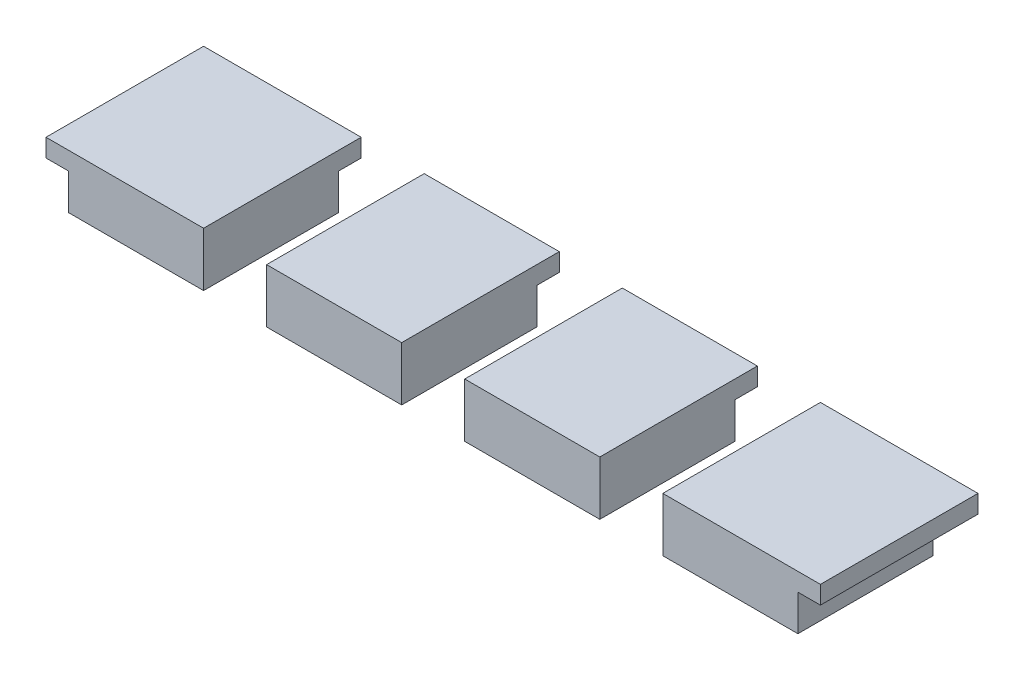
SolidWorks part; units mm, degrees
ref_plane "Front Plane" through (0, 0, 0) normal (0, 0, 1) x (1, 0, 0)
ref_plane "Top Plane" through (0, 0, 0) normal (0, 1, 0) x (1, 0, 0)
ref_plane "Right Plane" through (0, 0, 0) normal (1, 0, 0) x (0, 0, -1)
sketch "Sketch1" plane through (0, 0, 0) normal (0, 1, 0) x (1, 0, 0)
  line L1 (-39.05, -27.95) -> (39.05, -27.95)
  line L2 (-39.05, -27.95) -> (-39.05, 27.95)
  line L3 (-39.05, 27.95) -> (39.05, 27.95)
  line L4 (39.05, -27.95) -> (39.05, 27.95)
  line L5 (-39.05, -27.95) -> (39.05, 27.95) construction
  line L6 (-39.05, 27.95) -> (39.05, -27.95) construction
  point P0 (0, 0)
extrude "Boss-Extrude1" add sketch "Sketch1" along normal blind 3
sketch "Sketch2" plane through (0, 3, 0) normal (0, 1, 0) x (1, 0, 0)
  circle A0 centre (-35.9, 20.9) radius 1.25
  circle A1 centre (-35.9, -24.8) radius 1.25
  circle A2 centre (35.9, -24.8) radius 1.25
  circle A3 centre (35.9, 24.8) radius 1.25
extrude "Cut-Extrude1" cut sketch "Sketch2" against normal blind 68
sketch "Sketch3" plane through (0, 3, 0) normal (0, 1, 0) x (1, 0, 0)
  line L0 (-39.05, -27.95) -> (39.05, -27.95) construction
  line L5 (-31.15, -27.95) -> (8.45, -27.95)
  line L6 (-31.15, -27.95) -> (-31.15, -12.75)
  line L7 (-31.15, -12.75) -> (8.45, -12.75)
  line L8 (8.45, -27.95) -> (8.45, -12.75)
  line L13 (27.35, -17.65) -> (15.85, -17.65)
  line L14 (27.35, -17.65) -> (27.35, -27.95)
  line L15 (27.35, -27.95) -> (15.85, -27.95)
  line L16 (15.85, -17.65) -> (15.85, -27.95)
  line L18 (-39.05, 27.95) -> (39.05, 27.95)
  line L19 (-39.05, 27.95) -> (-39.05, -27.95)
  line L20 (-39.05, -27.95) -> (39.05, -27.95)
  line L21 (39.05, 27.95) -> (39.05, -27.95)
  line L22 (-31.15, -27.95) -> (-25.45, -27.95)
  line L23 (-31.15, -27.95) -> (-31.15, -20.45)
  line L24 (-31.15, -20.45) -> (-25.45, -20.45)
  line L25 (-25.45, -27.95) -> (-25.45, -20.45)
  line L26 (8.45, -27.95) -> (2.75, -27.95)
  line L27 (8.45, -27.95) -> (8.45, -20.45)
  line L28 (8.45, -20.45) -> (2.75, -20.45)
  line L29 (2.75, -27.95) -> (2.75, -20.45)
  line L30 (2.75, -27.95) -> (-6.65, -27.95)
  line L31 (2.75, -27.95) -> (2.75, -20.45)
  line L32 (2.75, -20.45) -> (-6.65, -20.45)
  line L33 (-6.65, -27.95) -> (-6.65, -20.45)
  line L34 (-25.45, -27.95) -> (-16.05, -27.95)
  line L35 (-25.45, -27.95) -> (-25.45, -20.45)
  line L36 (-25.45, -20.45) -> (-16.05, -20.45)
  line L37 (-16.05, -27.95) -> (-16.05, -20.45)
  circle A0 centre (35.9, 24.8) radius 1.25
  circle A1 centre (35.9, -24.8) radius 1.25
  circle A2 centre (-35.9, -24.8) radius 1.25
  circle A3 centre (-35.9, 20.9) radius 1.25
  circle A4 centre (2.75, -20.45) radius 4
  circle A5 centre (-6.65, -20.45) radius 4
  circle A6 centre (-16.05, -20.45) radius 4
  circle A7 centre (-25.45, -20.45) radius 4
sketch "Sketch4" plane through (0, 0, 0) normal (0, -1, 0) x (-1, 0, 0)
  line L0 (0, -27.95) -> (0, -29.95) construction
  line L1 (39.05, 27.95) -> (-39.05, 27.95)
  line L2 (39.05, 27.95) -> (39.05, -27.95)
  line L3 (39.05, -27.95) -> (-39.05, -27.95)
  line L4 (-39.05, 27.95) -> (-39.05, -27.95)
  line L5 (39.05, 27.95) -> (-39.05, -27.95) construction
  line L6 (39.05, -27.95) -> (-39.05, 27.95) construction
  line L7 (41.05, 29.95) -> (-41.05, 29.95)
  line L8 (41.05, 29.95) -> (41.05, -29.95)
  line L9 (41.05, -29.95) -> (-41.05, -29.95)
  line L10 (-41.05, 29.95) -> (-41.05, -29.95)
  line L11 (41.05, 29.95) -> (-41.05, -29.95) construction
  line L12 (41.05, -29.95) -> (-41.05, 29.95) construction
  line L13 (-39.05, 0) -> (-41.05, 0) construction
  point P0 (0, 0)
  point P7 (0, 0)
extrude "Boss-Extrude3" add sketch "Sketch4" against normal blind 3
sketch "Sketch6" plane through (0, 3, 0) normal (0, 1, 0) x (1, 0, 0)
  circle A0 centre (-35.9, -24.8) radius 1.25
  circle A1 centre (35.9, -24.8) radius 1.25
  circle A2 centre (35.9, 24.8) radius 1.25
  circle A3 centre (-35.9, 20.9) radius 1.25
  circle A4 centre (-35.9, 20.9) radius 3
  circle A5 centre (35.9, 24.8) radius 3
  circle A6 centre (35.9, -24.8) radius 3
  circle A7 centre (-35.9, -24.8) radius 3
extrude "Boss-Extrude4" add sketch "Sketch6" along normal blind 3.5
sketch "Sketch7" plane through (0, 0, 0) normal (0, -1, 0) x (-1, 0, 0)
  line L1 (-41.05, 29.95) -> (41.05, 29.95)
  line L2 (-41.05, 29.95) -> (-41.05, 46.15)
  line L3 (-41.05, 46.15) -> (41.05, 46.15)
  line L4 (41.05, 29.95) -> (41.05, 46.15)
extrude "Boss-Extrude5" add sketch "Sketch7" against normal blind 3
sketch "Sketch8" plane through (0, 0, -46.15) normal (0, 0, -1) x (-1, 0, 0)
  line L1 (-41.05, 0) -> (41.05, 0)
  line L2 (-41.05, 0) -> (-41.05, 50.5)
  line L3 (-41.05, 50.5) -> (41.05, 50.5)
  line L4 (41.05, 0) -> (41.05, 50.5)
extrude "Boss-Extrude6" add sketch "Sketch8" along normal blind 3
sketch "Sketch10" plane through (41.05, 0, 0) normal (1, 0, 0) x (0, 0, -1)
  line L1 (46.15, 50.5) -> (49.15, 50.5)
  line L2 (46.15, 50.5) -> (46.15, 0)
  line L3 (46.15, 0) -> (49.15, 0)
  line L4 (49.15, 50.5) -> (49.15, 0)
  line L5 (-29.95, 0) -> (46.15, 0)
  line L6 (-29.95, 0) -> (-29.95, 3)
  line L7 (-29.95, 3) -> (46.15, 3)
  line L8 (46.15, 0) -> (46.15, 3)
  line M1 (-29.95, 0) -> (49.15, 0)
  line M5 (46.15, 3) -> (-29.95, 3)
  line M6 (-29.95, 3) -> (-29.95, 0)
extrude "Boss-Extrude7" add sketch "Sketch10" along normal blind 20 contours L2 M5 M6 M1
sketch "Sketch12" plane through (-41.05, 0, 0) normal (-1, 0, 0) x (0, 0, 1)
  line L1 (-49.15, 50.5) -> (29.95, 50.5)
  line L2 (-49.15, 50.5) -> (-49.15, 0)
  line L3 (-49.15, 0) -> (29.95, 0)
  line L4 (29.95, 50.5) -> (29.95, 0)
extrude "Boss-Extrude8" add sketch "Sketch12" along normal blind 3
sketch "Sketch17" plane through (0, 0, 29.95) normal (0, 0, 1) x (1, 0, 0)
  line L1 (-44.05, 50.5) -> (61.05, 50.5)
  line L2 (-44.05, 50.5) -> (-44.05, 0)
  line L3 (-44.05, 0) -> (61.05, 0)
  line L4 (61.05, 50.5) -> (61.05, 0)
extrude "Boss-Extrude13" add sketch "Sketch17" against normal blind 2 and the other way blind 1
sketch "Sketch18" plane through (0, 0, 27.95) normal (0, 0, -1) x (-1, 0, 0)
  line L0 (-61.05, 3) -> (-61.05, 50.5) construction
  line L1 (41.05, 3) -> (-61.05, 3)
  line L2 (41.05, 3) -> (41.05, 6.5)
  line L4 (-61.05, 3) -> (-61.05, 6.5)
  line L10 (-8.45, 8.1) -> (-8.45, 13.1) construction
  line L19 (-8.45, 8.1) -> (-8.45, 22.1) construction
  line L21 (-8.45, 22.1) -> (31.15, 22.1)
  line L22 (-8.45, 22.1) -> (-8.45, 13.1)
  line L23 (-8.45, 13.1) -> (31.15, 13.1)
  line L24 (31.15, 22.1) -> (31.15, 13.1)
  line L31 (-25.35, 8.1) -> (-17.85, 11.8) construction
  line L32 (-25.35, 11.8) -> (-17.85, 8.1) construction
  line L38 (-27.35, 6.1) -> (-15.85, 6.1)
  line L39 (-27.35, 6.1) -> (-27.35, 13.8)
  line L40 (-27.35, 13.8) -> (-15.85, 13.8)
  line L41 (-15.85, 6.1) -> (-15.85, 13.8)
  line L42 (-27.35, 6.1) -> (-15.85, 13.8) construction
  line L43 (-27.35, 13.8) -> (-15.85, 6.1) construction
  point P7 (-21.6, 9.95)
  point P8 (-21.6, 9.95)
  point P27 (-21.6, 9.95)
  point P32 (-21.6, 9.95)
extrude "Cut-Extrude4" cut sketch "Sketch18" against normal blind 9 contours L38 L41 L40 L39 | L24 L21 L22 L23
sketch "Sketch19" plane through (61.05, 0, 0) normal (1, 0, 0) x (0, 0, -1)
  line L1 (-30.95, 50.5) -> (49.15, 50.5)
  line L2 (-30.95, 50.5) -> (-30.95, 0)
  line L3 (-30.95, 0) -> (49.15, 0)
  line L4 (49.15, 50.5) -> (49.15, 0)
extrude "Boss-Extrude14" add sketch "Sketch19" along normal blind 3
sketch "Sketch20" plane through (61.05, 0, 0) normal (-1, 0, 0) x (0, 0, 1)
  line L0 (-34.985, 3) -> (-34.985, 5) construction
  line L1 (-46.15, 3) -> (27.95, 3) construction
  line L2 (-46.15, 21.4946) -> (-44.15, 21.4946) construction
  line L3 (-46.15, 50.5) -> (-46.15, 3) construction
  line L4 (-44.15, 45) -> (-4.15, 5) construction
  line L14 (-39.9, 9.25) -> (-8.4, 40.75) construction
  line L15 (-39.9, 40.75) -> (-8.4, 9.25) construction
  circle A0 centre (-24.15, 25) radius 19
  circle A1 centre (-8.4, 40.75) radius 1.5
  circle A2 centre (-39.9, 40.75) radius 1.5
  circle A3 centre (-8.4, 9.25) radius 1.5
  circle A4 centre (-39.9, 9.25) radius 1.5
extrude "Cut-Extrude5" cut sketch "Sketch20" against normal blind 3
sketch "Sketch22" plane through (-41.05, 0, 0) normal (1, 0, 0) x (0, 0, -1)
  line L0 (46.15, 3) -> (27.95, 3) construction
  line L1 (-27.95, 3) -> (46.15, 3) construction
  line L2 (27.95, 3) -> (9.95, 3) construction
  line L3 (46.15, 26.75) -> (44.15, 26.75) construction
  line L4 (46.15, 3) -> (46.15, 50.5) construction
  line L5 (9.95, 45.5) -> (9.95, 36.125) construction
  line L6 (-27.95, 50.5) -> (46.15, 50.5) construction
  line L7 (44.15, 3) -> (44.15, 50.5) construction
  line L8 (18.5, 50.5) -> (18.5, 3) construction
  line L9 (9.95, 50.5) -> (18.5, 50.5) construction
  line L10 (27.05, 50.5) -> (27.05, 3) construction
  line L11 (18.5, 50.5) -> (27.05, 50.5) construction
  line L12 (35.6, 50.5) -> (35.6, 3) construction
  line L13 (27.05, 50.5) -> (35.6, 50.5) construction
  line L14 (35.6, 50.5) -> (44.15, 50.5) construction
  line L15 (14.225, 50.5) -> (14.225, 3) construction
  line L16 (22.775, 50.5) -> (22.775, 3) construction
  line L17 (31.325, 50.5) -> (31.325, 3) construction
  line L18 (39.875, 50.5) -> (39.875, 3) construction
  line L19 (9.95, 26.75) -> (44.15, 26.75) construction
  line L20 (9.95, 36.125) -> (9.95, 26.75) construction
  line L21 (9.95, 45.5) -> (44.15, 45.5) construction
  line L22 (9.95, 8) -> (44.15, 8) construction
  line L23 (9.95, 17.375) -> (44.15, 17.375) construction
  line L24 (9.95, 36.125) -> (44.15, 36.125) construction
  line L25 (9.95, 26.75) -> (9.95, 17.375) construction
  line L26 (9.95, 17.375) -> (9.95, 8) construction
  line L27 (9.95, 40.8125) -> (44.15, 40.8125) construction
  line L28 (9.95, 31.4375) -> (44.15, 31.4375) construction
  line L29 (9.95, 22.0625) -> (44.15, 22.0625) construction
  line L30 (9.95, 12.6875) -> (44.15, 12.6875) construction
  circle A0 centre (14.225, 12.6875) radius 2.5
  circle A1 centre (14.225, 22.0625) radius 2.5
  circle A2 centre (18.5, 17.375) radius 2.5
  circle A3 centre (22.775, 22.0625) radius 2.5
  circle A4 centre (22.775, 12.6875) radius 2.5
  circle A5 centre (14.225, 31.4375) radius 2.5
  circle A6 centre (18.5, 26.75) radius 2.5
  circle A7 centre (22.775, 31.4375) radius 2.5
  circle A8 centre (18.5, 36.125) radius 2.5
  circle A9 centre (14.225, 40.8125) radius 2.5
  circle A10 centre (22.775, 40.8125) radius 2.5
  circle A11 centre (27.05, 36.125) radius 2.5
  circle A12 centre (31.325, 40.8125) radius 2.5
  circle A13 centre (39.875, 40.8125) radius 2.5
  circle A14 centre (35.6, 36.125) radius 2.5
  circle A15 centre (39.875, 31.4375) radius 2.5
  circle A16 centre (31.325, 31.4375) radius 2.5
  circle A17 centre (27.05, 26.75) radius 2.5
  circle A18 centre (31.325, 22.0625) radius 2.5
  circle A19 centre (39.875, 22.0625) radius 2.5
  circle A20 centre (35.6, 26.75) radius 2.5
  circle A21 centre (27.05, 17.375) radius 2.5
  circle A22 centre (31.325, 12.6875) radius 2.5
  circle A23 centre (39.875, 12.6875) radius 2.5
  circle A24 centre (35.6, 17.375) radius 2.5
  circle A26 centre (18.5, 8) radius 2.5
  circle A27 centre (27.05, 8) radius 2.5
  circle A28 centre (35.6, 8) radius 2.5
extrude "Cut-Extrude6" cut sketch "Sketch22" against normal blind 3
sketch "Sketch23" plane through (64.05, 0, 0) normal (1, 0, 0) x (0, 0, -1)
  circle A0 centre (8.4, 9.25) radius 1.5
  circle A1 centre (39.9, 40.75) radius 1.5
extrude "Boss-Extrude16" add sketch "Sketch23" against normal blind 3
sketch "Sketch25" plane through (0, 0, 30.95) normal (0, 0, 1) x (1, 0, 0)
  line L1 (-44.05, 50.5) -> (64.05, 50.5)
  line L2 (-44.05, 50.5) -> (-44.05, 0)
  line L3 (-44.05, 0) -> (64.05, 0)
  line L4 (64.05, 50.5) -> (64.05, 0)
extrude "Cut-Extrude8" cut sketch "Sketch25" against normal blind 0.5
sketch "Sketch26" plane through (64.05, 0, 0) normal (1, 0, 0) x (0, 0, -1)
  line L1 (-30.45, 50.5) -> (49.15, 50.5)
  line L2 (-30.45, 50.5) -> (-30.45, 0)
  line L3 (-30.45, 0) -> (49.15, 0)
  line L4 (49.15, 50.5) -> (49.15, 0)
extrude "Cut-Extrude9" cut sketch "Sketch26" against normal blind 0.5
sketch "Sketch27" plane through (0, 0, -49.15) normal (0, 0, -1) x (-1, 0, 0)
  line L1 (-63.55, 50.5) -> (44.05, 50.5)
  line L2 (-63.55, 50.5) -> (-63.55, 0)
  line L3 (-63.55, 0) -> (44.05, 0)
  line L4 (44.05, 50.5) -> (44.05, 0)
extrude "Cut-Extrude10" cut sketch "Sketch27" against normal blind 0.5
sketch "Sketch28" plane through (-44.05, 0, 0) normal (-1, 0, 0) x (0, 0, 1)
  line L1 (-48.65, 50.5) -> (30.45, 50.5)
  line L2 (-48.65, 50.5) -> (-48.65, 0)
  line L3 (-48.65, 0) -> (30.45, 0)
  line L4 (30.45, 50.5) -> (30.45, 0)
extrude "Cut-Extrude11" cut sketch "Sketch28" against normal blind 0.5
sketch "Sketch30" plane through (0, 50.5, 0) normal (0, 1, 0) x (1, 0, 0)
  line L0 (61.05, 46.15) -> (-41.05, -27.95) construction
  line L1 (10, -27.45) -> (10, -27.95) construction
  line L2 (-40.55, 45.65) -> (60.55, 45.65)
  line L3 (-40.55, 45.65) -> (-40.55, -27.45)
  line L4 (-40.55, -27.45) -> (60.55, -27.45)
  line L5 (60.55, 45.65) -> (60.55, -27.45)
  line L6 (-40.55, 45.65) -> (60.55, -27.45) construction
  line L7 (-40.55, -27.45) -> (60.55, 45.65) construction
  line L8 (61.05, -27.95) -> (-41.05, -27.95) construction
  line L9 (60.55, 9.1) -> (61.05, 9.1) construction
  line L10 (61.05, 46.15) -> (61.05, -27.95) construction
  point P4 (10, 9.1)
extrude "Boss-Extrude17" add sketch "Sketch30" along normal blind 2 and the other way blind 6 separate body
sketch "Sketch31" plane through (0, 3, 0) normal (0, 1, 0) x (1, 0, 0)
  line L1 (-31.15, -12.75) -> (8.45, -12.75)
  line L2 (-31.15, -12.75) -> (-31.15, -27.95)
  line L3 (-31.15, -27.95) -> (8.45, -27.95)
  line L4 (8.45, -12.75) -> (8.45, -27.95)
extrude "Cut-Extrude12" cut sketch "Sketch31" against normal blind 18
sketch "Sketch32" plane through (0, 0, 0) normal (0, -1, 0) x (1, 0, 0)
  circle A0 centre (2.73, 16.5811) radius 4
  circle A1 centre (-6.6072, 16.5811) radius 4
  circle A2 centre (-16.03, 16.55) radius 4
  circle A3 centre (-25.43, 16.55) radius 4
extrude "Cut-Extrude13" cut sketch "Sketch32" against normal blind 788
sketch "Sketch35" plane through (0, 0, 30.45) normal (0, 0, 1) x (1, 0, 0)
  line L0 (10, 50.5) -> (10, 44.5) construction
  line L1 (63.55, 50.5) -> (-43.55, 50.5) construction
  line L2 (-43.55, 0) -> (-43.55, 50.5) construction
  line L3 (-43.55, 44.5) -> (84.6873, 44.5)
  line L4 (-43.55, 44.5) -> (-43.55, -56.9173)
  line L5 (-43.55, -56.9173) -> (84.6873, -56.9173)
  line L6 (84.6873, 44.5) -> (84.6873, -56.9173)
extrude "Cut-Extrude16" cut sketch "Sketch35" against normal blind 109
sketch "Sketch36" plane through (0, 50.5, 0) normal (0, 1, 0) x (1, 0, 0)
  line L1 (-43.55, 48.65) -> (63.55, 48.65)
  line L2 (-43.55, 48.65) -> (-43.55, -30.45)
  line L3 (-43.55, -30.45) -> (63.55, -30.45)
  line L4 (63.55, 48.65) -> (63.55, -30.45)
  line L5 (61.05, -27.95) -> (-41.05, -27.95)
  line L6 (61.05, -27.95) -> (61.05, 46.15)
  line L7 (61.05, 46.15) -> (-41.05, 46.15)
  line L8 (-41.05, -27.95) -> (-41.05, 46.15)
extrude "Boss-Extrude18" add sketch "Sketch36" along normal blind 2
sketch "Sketch37" plane through (0, 44.5, 0) normal (0, -1, 0) x (-1, 0, 0)
  line L1 (43.55, -30.45) -> (-63.55, -30.45)
  line L2 (43.55, -30.45) -> (43.55, 48.65)
  line L3 (43.55, 48.65) -> (-63.55, 48.65)
  line L4 (-63.55, -30.45) -> (-63.55, 48.65)
  line L5 (-61.05, 46.15) -> (41.05, 46.15)
  line L6 (-61.05, 46.15) -> (-61.05, -27.95)
  line L7 (-61.05, -27.95) -> (41.05, -27.95)
  line L8 (41.05, 46.15) -> (41.05, -27.95)
extrude "Cut-Extrude17" cut sketch "Sketch37" against normal blind 6
sketch "Sketch38" plane through (0, 52.5, 0) normal (0, 1, 0) x (1, 0, 0)
  line L1 (61.05, -27.95) -> (-41.05, -27.95)
  line L2 (61.05, -27.95) -> (61.05, 46.15)
  line L3 (61.05, 46.15) -> (-41.05, 46.15)
  line L4 (-41.05, -27.95) -> (-41.05, 46.15)
  line L5 (-32.3027, -6.1655) -> (10, -6.1655)
  line L6 (-32.3027, -6.1655) -> (-32.3027, -24.9297)
  line L7 (-32.3027, -24.9297) -> (10, -24.9297)
  line L8 (10, -6.1655) -> (10, -24.9297)
extrude "Boss-Extrude19" add sketch "Sketch38" against normal blind 2
sketch "Sketch39" plane through (0, 44.5, 0) normal (0, -1, 0) x (-1, 0, 0)
  line L0 (40.55, -27.45) -> (-60.55, 45.65) construction
  line L5 (-10, 45.65) -> (-10, 44.15) construction
  line L6 (-60.55, 9.1) -> (-59.05, 9.1) construction
  line L7 (-10, -27.45) -> (-10, -25.95) construction
  line L9 (39.05, 44.15) -> (-59.05, 44.15)
  line L10 (39.05, 44.15) -> (39.05, -25.95)
  line L11 (39.05, -25.95) -> (-59.05, -25.95)
  line L12 (-59.05, 44.15) -> (-59.05, -25.95)
  line L13 (39.05, 44.15) -> (-59.05, -25.95) construction
  line L14 (39.05, -25.95) -> (-59.05, 44.15) construction
  point P12 (-10, 9.1)
extrude "Cut-Extrude18" cut sketch "Sketch39" against normal blind 6
sketch "Sketch40" plane through (0, 50.5, 0) normal (0, -1, 0) x (-1, 0, 0)
  line L0 (25.43, -11.1817) -> (-2.73, -11.2439)
  line L1 (-2.73, -21.9183) -> (25.43, -21.9183)
  circle A0 centre (-2.73, -16.5811) radius 4
  circle A1 centre (6.6072, -16.5811) radius 4
  circle A3 centre (25.43, -16.55) radius 4
  circle A4 centre (-2.73, -16.5811) radius 5.3372
  circle A5 centre (25.43, -16.55) radius 5.3683
  circle A6 centre (16.03, -16.55) radius 4
  circle M4 centre (16.03, -16.55) radius 4
  circle M5 centre (-2.73, -16.5811) radius 4
  circle M10 centre (6.6072, -16.5811) radius 4
  circle M11 centre (25.43, -16.55) radius 4
extrude "Boss-Extrude21" add sketch "Sketch40" along normal blind 20 contours A5 L0 A4 L1 M10 M4 | A4 M5 | L0 A5 M11
sketch "Sketch43" plane through (59.05, 0, 0) normal (-1, 0, 0) x (0, 0, 1)
  line L5 (-0.65, 46) -> (-44.15, 46)
  line L6 (-0.65, 46) -> (-0.65, 44.5)
  line L7 (-0.65, 44.5) -> (-44.15, 44.5)
  line L8 (-44.15, 46) -> (-44.15, 44.5)
extrude "Cut-Extrude19" cut sketch "Sketch43" against normal blind 20
sketch "Sketch44" plane through (0, 0, -44.15) normal (0, 0, 1) x (1, 0, 0)
  line L0 (-39.05, 44.5) -> (60.55, 44.5) construction
  line L1 (60.55, 46) -> (38.55, 46)
  line L2 (60.55, 46) -> (60.55, 44.5)
  line L3 (60.55, 44.5) -> (38.55, 44.5)
  line L4 (38.55, 46) -> (38.55, 44.5)
extrude "Cut-Extrude20" cut sketch "Sketch44" against normal blind 20
fillet "Fillet1" radius 3 4 edges at (-30.7983, 50.5, 16.55) (-11.35, 50.5, 21.9183) (8.0672, 50.5, 16.5811) (-11.35, 50.5, 11.2128)
sketch "Sketch45" plane through (0, 50.5, 0) normal (0, -1, 0) x (-1, 0, 0)
  line L1 (39.05, -25.95) -> (-34.2088, -25.95)
  line L2 (39.05, -25.95) -> (39.05, 18.7182)
  line L3 (39.05, 18.7182) -> (-34.2088, 18.7182)
  line L4 (-34.2088, -25.95) -> (-34.2088, 18.7182)
extrude "Cut-Extrude21" cut sketch "Sketch45" along normal blind 63
extrude "Cut-Extrude22" cut sketch "Sketch3" against normal blind 374 and the other way blind 380 contours L36 A7 L24 | L24 A7 L35 | L35 A7 L36 | L36 A6 L37 | L37 A6 L36 | L32 A5 L33 | L33 A5 L32 | L32 A4 L31 | L31 A4 L28 | L28 A4 L32
sketch "Sketch49" plane through (0, 50.5, 0) normal (0, -1, 0) x (-1, 0, 0)
  circle A0 centre (25.45, -20.45) radius 4
  circle A1 centre (16.05, -20.45) radius 4
  circle A2 centre (6.65, -20.45) radius 4
  circle A3 centre (-2.75, -20.45) radius 4
  circle A4 centre (-2.73, -16.5811) radius 4
  circle A5 centre (6.6072, -16.5811) radius 4
  circle A6 centre (16.03, -16.55) radius 4
  circle A7 centre (25.43, -16.55) radius 4
  arc M3 (21.9476, -18.5179) -> (28.9324, -18.4821) centre (25.43, -16.55) cw
  arc M5 (12.5476, -18.5179) -> (19.5324, -18.4821) centre (16.03, -16.55) cw
  arc M7 (3.1277, -18.5543) -> (10.1294, -18.4768) centre (6.6072, -16.5811) cw
  arc M9 (-6.2411, -18.4974) -> (0.7611, -18.5336) centre (-2.73, -16.5811) cw
extrude "Boss-Extrude23" add sketch "Sketch49" against normal blind 2 contours A3 M9 | A2 M7 | A1 M5 | A0 M3
sketch "Sketch50" plane through (0, 50.5, 0) normal (0, -1, 0) x (-1, 0, 0)
  line L0 (25.45, -14.95) -> (-2.75, -14.95)
  line L1 (-2.75, -25.95) -> (25.45, -25.95)
  circle A0 centre (-2.75, -20.45) radius 5.5
  circle A1 centre (25.45, -20.45) radius 5.5
  circle M1 centre (25.45, -20.45) radius 4
  circle M2 centre (16.05, -20.45) radius 4
  circle M3 centre (6.65, -20.45) radius 4
  circle M4 centre (-2.75, -20.45) radius 4
  line M8 (-59.05, -25.95) -> (39.05, -25.95)
extrude "Boss-Extrude24" add sketch "Sketch50" along normal blind 23 contours A1 L0 A0 M3 M8 M2 | A1 M2 M1 | A0 M3 M4
fillet "Fillet2" radius 3 3 edges at (-30.95, 50.5, 20.45) (-11.35, 50.5, 14.95) (8.25, 50.5, 20.45)
sketch "Sketch51" plane through (0, 0, -45.65) normal (0, 0, -1) x (-1, 0, 0)
  line L0 (-60.55, 46) -> (-60.55, 50.5) construction
  line L1 (-38.55, 46) -> (-60.55, 46)
  line L2 (-38.55, 46) -> (-38.55, 46.5)
  line L3 (-38.55, 46.5) -> (-60.55, 46.5)
  line L4 (-60.55, 46) -> (-60.55, 46.5)
extrude "Cut-Extrude23" cut sketch "Sketch51" against normal blind 23
sketch "Sketch52" plane through (60.55, 0, 0) normal (1, 0, 0) x (0, 0, -1)
  line L1 (22.65, 46.5) -> (0.65, 46.5)
  line L2 (22.65, 46.5) -> (22.65, 46)
  line L3 (22.65, 46) -> (0.65, 46)
  line L4 (0.65, 46.5) -> (0.65, 46)
extrude "Cut-Extrude24" cut sketch "Sketch52" against normal blind 23
sketch "Sketch53" plane through (0, 52.5, 0) normal (0, 1, 0) x (1, 0, 0)
  line L0 (63.55, -24.45) -> (6.75, -24.45) construction
  line L1 (63.55, -30.45) -> (63.55, 48.65) construction
  line L2 (6.75, -24.45) -> (6.75, -20.45) construction
  line L3 (6.75, -20.45) -> (6.75, -16.45) construction
  line L4 (6.75, -16.45) -> (63.55, -16.45) construction
  line L5 (33.65, -20.45) -> (36.65, -20.45)
  line L6 (35.15, -24.45) -> (35.15, -16.45) construction
  line L7 (36.65, -20.45) -> (44.65, -20.45) construction
  line L8 (44.65, -20.45) -> (47.65, -20.45) construction
  line L9 (47.65, -20.45) -> (55.65, -20.45) construction
  line L10 (33.65, -20.45) -> (25.65, -20.45) construction
  line L11 (25.65, -20.45) -> (22.65, -20.45) construction
  line L12 (22.65, -20.45) -> (14.65, -20.45) construction
  line L14 (22.65, -24.45) -> (14.65, -24.45)
  line L15 (22.65, -24.45) -> (22.65, -16.45)
  line L16 (22.65, -16.45) -> (14.65, -16.45)
  line L17 (14.65, -24.45) -> (14.65, -16.45)
  line L18 (22.65, -24.45) -> (14.65, -16.45) construction
  line L19 (22.65, -16.45) -> (14.65, -24.45) construction
  line L20 (33.65, -24.45) -> (25.65, -24.45)
  line L21 (33.65, -24.45) -> (33.65, -16.45)
  line L22 (33.65, -16.45) -> (25.65, -16.45)
  line L23 (25.65, -24.45) -> (25.65, -16.45)
  line L24 (33.65, -24.45) -> (25.65, -16.45) construction
  line L25 (33.65, -16.45) -> (25.65, -24.45) construction
  line L26 (44.65, -24.45) -> (36.65, -24.45)
  line L27 (44.65, -24.45) -> (44.65, -16.45)
  line L28 (44.65, -16.45) -> (36.65, -16.45)
  line L29 (36.65, -24.45) -> (36.65, -16.45)
  line L30 (44.65, -24.45) -> (36.65, -16.45) construction
  line L31 (44.65, -16.45) -> (36.65, -24.45) construction
  line L32 (55.65, -24.45) -> (47.65, -24.45)
  line L33 (55.65, -24.45) -> (55.65, -16.45)
  line L34 (55.65, -16.45) -> (47.65, -16.45)
  line L35 (47.65, -24.45) -> (47.65, -16.45)
  line L36 (55.65, -24.45) -> (47.65, -16.45) construction
  line L37 (55.65, -16.45) -> (47.65, -24.45) construction
  circle A0 centre (2.75, -20.45) radius 4 construction
  point P10 (18.65, -20.45)
  point P14 (35.15, -20.45)
  point P25 (29.65, -20.45)
  point P30 (40.65, -20.45)
  point P35 (51.65, -20.45)
extrude "Cut-Extrude25" cut sketch "Sketch53" against normal blind 23 contours L35 L32 L33 L34 | L29 L26 L27 L28 | L23 L20 L21 L22 | L17 L14 L15 L16
sketch "Sketch54" plane through (0, 27.5, 0) normal (0, -1, 0) x (-1, 0, 0)
  line L0 (-2.75, -14.95) -> (25.45, -14.95)
  line L2 (35.5013, -14.95) -> (-14.2013, -14.95)
  line L3 (35.5013, -14.95) -> (35.5013, -25.95)
  line L4 (35.5013, -25.95) -> (-14.2013, -25.95)
  line L5 (-14.2013, -14.95) -> (-14.2013, -25.95)
  line L6 (35.5013, -14.95) -> (-14.2013, -25.95) construction
  line L7 (35.5013, -25.95) -> (-14.2013, -14.95) construction
  line L8 (35.5013, -14.95) -> (-14.2013, -14.95)
  line L9 (35.5013, -14.95) -> (35.5013, -4.0672)
  line L10 (35.5013, -4.0672) -> (-14.2013, -4.0672)
  line L11 (-14.2013, -14.95) -> (-14.2013, -4.0672)
  circle A0 centre (25.45, -20.45) radius 5.5
  circle A1 centre (-2.75, -20.45) radius 5.5
  circle A2 centre (6.65, -20.45) radius 4 construction
  point P10 (10.65, -20.45)
  line M3 (25.45, -14.95) -> (-2.75, -14.95)
  arc M4 (-2.75, -14.95) -> (-2.75, -25.95) centre (-2.75, -20.45) ccw
  arc M6 (25.45, -25.95) -> (25.45, -14.95) centre (25.45, -20.45) ccw
extrude "Cut-Extrude26" cut sketch "Sketch54" against normal blind 23 contours L11 L2 L9 L10 M3 | L4 L3 L2 M6 | L2 L5 L4 M4
sketch "Sketch56" plane through (0, 50.5, 0) normal (0, -1, 0) x (1, 0, 0)
  line L0 (59.05, -44.15) -> (59.05, 25.95) construction
  line L1 (55.65, 24.45) -> (59.05, 24.45)
  line L2 (55.65, 24.45) -> (55.65, 25.95)
  line L3 (55.65, 25.95) -> (59.05, 25.95)
  line L4 (59.05, 24.45) -> (59.05, 25.95)
  line L5 (55.65, 24.45) -> (59.05, 24.45)
  line L6 (55.65, 24.45) -> (55.65, 16.45)
  line L7 (55.65, 16.45) -> (59.05, 16.45)
  line L8 (59.05, 24.45) -> (59.05, 16.45)
  line L10 (59.05, 16.45) -> (55.65, 16.45)
  line L11 (59.05, 16.45) -> (59.05, 14.95)
  line L12 (59.05, 14.95) -> (55.65, 14.95)
  line L13 (55.65, 16.45) -> (55.65, 14.95)
  line M9 (59.05, 25.95) -> (2.75, 25.95)
  line M16 (59.05, -44.15) -> (59.05, 25.95)
  line M19 (55.65, 24.45) -> (55.65, 16.45)
extrude "Boss-Extrude25" add sketch "Sketch56" along normal blind 6 contours L2 L1 M16 M9 | L7 L1 M19 M16 | L7 L13 L12 M16
sketch "Sketch58" plane through (0, 50.5, 0) normal (0, -1, 0) x (1, 0, 0)
  line L0 (55.65, 25.95) -> (2.75, 25.95) construction
  line L1 (14.65, 25.95) -> (9.75, 25.95)
  line L2 (14.65, 25.95) -> (14.65, 14.95)
  line L3 (14.65, 14.95) -> (9.75, 14.95)
  line L4 (9.75, 25.95) -> (9.75, 14.95)
sketch "Sketch59" plane through (0, 44.5, 0) normal (0, -1, 0) x (-1, 0, 0)
extrude "Boss-Extrude26" add sketch "Sketch58" along normal blind 6
sketch "Sketch61" plane through (0, 44.5, 0) normal (0, -1, 0) x (-1, 0, 0)
  line L0 (-14.65, -25.95) -> (-9.75, -25.95) construction
  line L1 (-55.65, -25.95) -> (-60.55, -25.95) construction
  line L2 (-60.55, -27.45) -> (-60.55, 0.65) construction
  line L3 (-58.1, -25.95) -> (-58.1, -14.95) construction
  line L4 (-59.05, -14.95) -> (-55.65, -14.95) construction
  line L5 (-12.2, -25.95) -> (-12.2, -14.95) construction
  line L6 (-9.75, -14.95) -> (-14.65, -14.95) construction
  line L7 (-12.2, -20.45) -> (-58.1, -20.45) construction
  line L8 (-58.15, -20.45) -> (-12.15, -20.45)
  circle A0 centre (-58.15, -20.45) radius 1
  circle A1 centre (-12.15, -20.45) radius 1
  point P22 (-35.15, -20.45)
extrude "Cut-Extrude27" cut sketch "Sketch61" against normal blind 6
sketch "Sketch62" plane through (0, 44.5, 0) normal (0, -1, 0) x (-1, 0, 0)
  line L1 (-55.65, -14.95) -> (-59.05, -14.95)
  line L2 (-55.65, -14.95) -> (-55.65, 0.65)
  line L3 (-55.65, 0.65) -> (-59.05, 0.65)
  line L4 (-59.05, -14.95) -> (-59.05, 0.65)
extrude "Boss-Extrude27" add sketch "Sketch62" against normal blind 6
sketch "Sketch64" plane through (0, 44.5, 0) normal (0, -1, 0) x (1, 0, 0)
  line L1 (9.75, 14.95) -> (14.65, 14.95)
  line L2 (9.75, 14.95) -> (9.75, 25.95)
  line L3 (9.75, 25.95) -> (14.65, 25.95)
  line L4 (14.65, 14.95) -> (14.65, 25.95)
  line L5 (55.65, -0.65) -> (60.55, -0.65)
  line L6 (55.65, -0.65) -> (55.65, 27.45)
  line L7 (55.65, 27.45) -> (60.55, 27.45)
  line L8 (60.55, -0.65) -> (60.55, 27.45)
  line L9 (55.65, 25.95) -> (-40.55, 25.95)
  line L10 (55.65, 25.95) -> (55.65, 27.45)
  line L11 (55.65, 27.45) -> (-40.55, 27.45)
  line L12 (-40.55, 25.95) -> (-40.55, 27.45)
  line L13 (-40.55, 25.95) -> (-39.05, 25.95)
  line L14 (-40.55, 25.95) -> (-40.55, -44.15)
  line L15 (-40.55, -44.15) -> (-39.05, -44.15)
  line L16 (-39.05, 25.95) -> (-39.05, -44.15)
  line L17 (-40.55, -44.15) -> (38.55, -44.15)
  line L18 (-40.55, -44.15) -> (-40.55, -45.65)
  line L19 (-40.55, -45.65) -> (38.55, -45.65)
  line L20 (38.55, -44.15) -> (38.55, -45.65)
  circle M1 centre (58.15, 20.45) radius 1
  circle M2 centre (12.15, 20.45) radius 1
  line M3 (14.65, 25.95) -> (55.65, 25.95)
  line M4 (55.65, 25.95) -> (55.65, -0.65)
  line M5 (55.65, -0.65) -> (60.55, -0.65)
  line M6 (60.55, -0.65) -> (60.55, 27.45)
  line M7 (60.55, 27.45) -> (-40.55, 27.45)
  line M8 (-40.55, 27.45) -> (-40.55, -45.65)
  line M9 (-40.55, -45.65) -> (38.55, -45.65)
  line M10 (38.55, -45.65) -> (38.55, -44.15)
  line M11 (38.55, -44.15) -> (-39.05, -44.15)
  line M12 (-39.05, -44.15) -> (-39.05, 25.95)
  line M13 (-39.05, 25.95) -> (-25.45, 25.95)
  line M14 (-25.45, 25.95) -> (2.75, 25.95)
  line M15 (2.75, 25.95) -> (9.75, 25.95)
  line M16 (9.75, 25.95) -> (9.75, 14.95)
  line M17 (9.75, 14.95) -> (14.65, 14.95)
  line M18 (14.65, 14.95) -> (14.65, 25.95)
extrude "Boss-Extrude28" add sketch "Sketch64" along normal blind 2 contours L3 M16 M17 M18 M2 | L6 M4 M5 M6 M7 M1 | L9 L3 L6 M13 M14 M15 M3 M7 M8 | L15 L9 M8 M12 | L15 M8 M9 M10 M11
sketch "Sketch65" plane through (0, 50.5, 0) normal (0, -1, 0) x (-1, 0, 0)
  line L0 (-2.75, -14.95) -> (-9.75, -14.95)
  line L1 (-9.75, -14.95) -> (-9.75, -25.95)
  line L2 (-9.75, -25.95) -> (-2.75, -25.95)
  arc A0 (-2.75, -14.95) -> (-2.75, -25.95) centre (-2.75, -20.45) ccw construction
  circle A1 centre (-2.75, -20.45) radius 5.5
  line M22 (-9.75, -14.95) -> (-9.75, -25.95)
  line M23 (-9.75, -25.95) -> (-2.75, -25.95)
  arc M24 (-2.75, -25.95) -> (-2.75, -14.95) centre (-2.75, -20.45) cw
extrude "Boss-Extrude29" add sketch "Sketch65" along normal blind 8 contours L0 M24 M22 M23
sketch "Sketch67" plane through (0, 52.5, 0) normal (0, 1, 0) x (1, 0, 0)
  line L1 (63.55, -30.45) -> (-43.55, -30.45)
  line L2 (63.55, -30.45) -> (63.55, 48.65)
  line L3 (63.55, 48.65) -> (-43.55, 48.65)
  line L4 (-43.55, -30.45) -> (-43.55, 48.65)
  line L5 (55.65, -24.45) -> (47.65, -24.45)
  line L6 (55.65, -24.45) -> (55.65, -16.45)
  line L7 (55.65, -16.45) -> (47.65, -16.45)
  line L8 (47.65, -24.45) -> (47.65, -16.45)
  line L9 (44.65, -24.45) -> (36.65, -24.45)
  line L10 (44.65, -24.45) -> (44.65, -16.45)
  line L11 (44.65, -16.45) -> (36.65, -16.45)
  line L12 (36.65, -24.45) -> (36.65, -16.45)
  line L13 (33.65, -24.45) -> (25.65, -24.45)
  line L14 (33.65, -24.45) -> (33.65, -16.45)
  line L15 (33.65, -16.45) -> (25.65, -16.45)
  line L16 (25.65, -24.45) -> (25.65, -16.45)
  line L17 (22.65, -24.45) -> (14.65, -24.45)
  line L18 (22.65, -24.45) -> (22.65, -16.45)
  line L19 (22.65, -16.45) -> (14.65, -16.45)
  line L20 (14.65, -24.45) -> (14.65, -16.45)
  circle A0 centre (2.75, -20.45) radius 4
  circle A1 centre (-6.65, -20.45) radius 4
  circle A2 centre (-16.05, -20.45) radius 4
  circle A3 centre (-25.45, -20.45) radius 4
extrude "Boss-Extrude30" add sketch "Sketch67" along normal blind 22
sketch "Sketch68" plane through (0, 50.5, 0) normal (0, -1, 0) x (1, 0, 0)
  line L0 (-39.05, -44.15) -> (59.05, -44.15) construction
  line L1 (59.05, -44.15) -> (14.65, -44.15)
  line L2 (59.05, -44.15) -> (59.05, 16.45)
  line L3 (59.05, 16.45) -> (14.65, 16.45)
  line L4 (14.65, -44.15) -> (14.65, 16.45)
  line L5 (14.65, 14.95) -> (-39.05, 14.95)
  line L6 (14.65, 14.95) -> (14.65, -44.15)
  line L7 (14.65, -44.15) -> (-39.05, -44.15)
  line L8 (-39.05, 14.95) -> (-39.05, -44.15)
  line L9 (-25.45, 25.95) -> (-39.05, 25.95) construction
  line L10 (-39.05, -44.15) -> (-30.95, -44.15)
  line L11 (-39.05, -44.15) -> (-39.05, 25.95)
  line L12 (-39.05, 25.95) -> (-30.95, 25.95)
  line L13 (-30.95, -44.15) -> (-30.95, 25.95)
  circle A0 centre (-25.45, 20.45) radius 5.5
  line M4 (33.65, 16.45) -> (25.65, 16.45)
  line M8 (44.65, 16.45) -> (36.65, 16.45)
  line M9 (14.65, 16.45) -> (14.65, 14.95)
  line M10 (14.65, 14.95) -> (-25.45, 14.95)
  arc M11 (-25.45, 14.95) -> (-25.45, 25.95) centre (-25.45, 20.45) cw
  line M12 (-25.45, 25.95) -> (-39.05, 25.95)
  line M13 (-39.05, 25.95) -> (-39.05, -44.15)
  line M14 (-39.05, -44.15) -> (59.05, -44.15)
  line M15 (59.05, -44.15) -> (59.05, -0.65)
  line M16 (59.05, -0.65) -> (55.65, -0.65)
  line M17 (55.65, -0.65) -> (55.65, 16.45)
  line M18 (55.65, 16.45) -> (47.65, 16.45)
  line M26 (22.65, 16.45) -> (14.65, 16.45)
extrude "Cut-Extrude28" cut sketch "Sketch68" against normal blind 22 contours L4 L3 M14 M15 M16 M17 M18 M8 M4 M26 M9 | L13 L7 L4 L5 M10 | L13 L5 M14 M13 | L5 L13 M12 M13 | L13 L5 M11 | L13 M11 M12
sketch "Sketch70" plane through (0, 72.5, 0) normal (0, -1, 0) x (1, 0, 0)
  line L0 (59.05, -44.15) -> (-39.05, -44.15) construction
  line L1 (10, -15.6) -> (10, -44.15) construction
  line L8 (50, 2.4) -> (-30, -33.6) construction
  line L14 (47.5, -0.1) -> (-27.5, -31.1) construction
  line L15 (47.5, -31.1) -> (-27.5, -0.1) construction
  circle A0 centre (47.5, -31.1) radius 1.25
  circle A1 centre (-27.5, -31.1) radius 1.25
  circle A2 centre (-27.5, -0.1) radius 1.25
  circle A3 centre (47.5, -0.1) radius 1.25
  point P8 (10, -15.6)
  point P13 (10, -15.6)
extrude "Cut-Extrude29" cut sketch "Sketch70" against normal blind 22
sketch "Sketch71" plane through (0, 72.5, 0) normal (0, -1, 0) x (1, 0, 0)
  line L1 (10, -33.6) -> (10, -15.1748) construction
  line L2 (50, 2.4) -> (-30, 2.4)
  line L3 (50, 2.4) -> (50, -33.6)
  line L4 (50, -33.6) -> (-30, -33.6)
  line L5 (-30, 2.4) -> (-30, -33.6)
  line L10 (46.0987, -2.6748) -> (-26.0987, -27.6748) construction
  line L11 (46.0987, -27.6748) -> (-26.0987, -2.6748) construction
  line L12 (41.5, -8.6748) -> (-21.5, -8.6748)
  line L13 (41.5, -8.6748) -> (41.5, -21.6748)
  line L14 (41.5, -21.6748) -> (-21.5, -21.6748)
  line L15 (-21.5, -8.6748) -> (-21.5, -21.6748)
  line L16 (41.5, -8.6748) -> (-21.5, -21.6748) construction
  line L17 (41.5, -21.6748) -> (-21.5, -8.6748) construction
  point P4 (10, -15.6)
extrude "Cut-Extrude30" cut sketch "Sketch71" against normal blind 22 contours L13 L12 L15 L14
sketch "Sketch72" plane through (0, 72.5, 0) normal (0, -1, 0) x (-1, 0, 0)
  line L0 (-41.5, 8.6748) -> (21.5, 21.6748) construction
  line L2 (-46.1, 2.6748) -> (26.1, 2.6748)
  line L3 (-46.1, 2.6748) -> (-46.1, 27.6748)
  line L4 (-46.1, 27.6748) -> (26.1, 27.6748)
  line L5 (26.1, 2.6748) -> (26.1, 27.6748)
  line L6 (-46.1, 2.6748) -> (26.1, 27.6748) construction
  line L7 (-46.1, 27.6748) -> (26.1, 2.6748) construction
  point P4 (-10, 15.1748)
extrude "Cut-Extrude31" cut sketch "Sketch72" against normal blind 1
sketch "Sketch73" plane through (0, 72.5, 0) normal (0, -1, 0) x (-1, 0, 0)
  line L0 (-46.1, 27.6748) -> (26.1, 2.6748) construction
  line L2 (-46.1, 2.6748) -> (26.1, 2.6748)
  line L3 (-46.1, 2.6748) -> (-46.1, 27.6748)
  line L4 (-46.1, 27.6748) -> (26.1, 27.6748)
  line L5 (26.1, 2.6748) -> (26.1, 27.6748)
  line L6 (-46.1, 2.6748) -> (26.1, 27.6748) construction
  line L7 (-46.1, 27.6748) -> (26.1, 2.6748) construction
  line L8 (27.5, 28.9995) -> (-47.5, 28.9995)
  line L9 (27.5, 28.9995) -> (27.5, 1.35)
  line L10 (27.5, 1.35) -> (-47.5, 1.35)
  line L11 (-47.5, 28.9995) -> (-47.5, 1.35)
  line L12 (27.5, 28.9995) -> (-47.5, 1.35) construction
  line L13 (27.5, 1.35) -> (-47.5, 28.9995) construction
  circle A0 centre (-47.5, 0.1) radius 1.25 construction
  circle A1 centre (-47.5, 0.1) radius 2.9308
  circle A2 centre (27.5, 0.1) radius 2.9308
  circle A3 centre (27.5, 31.1) radius 2.93
  circle A4 centre (-47.5, 31.1) radius 2.93
  circle A5 centre (-47.5, 31.1) radius 1.25
  circle A6 centre (27.5, 31.1) radius 1.25
  circle A7 centre (27.5, 0.1) radius 1.25
  circle A8 centre (-47.5, 0.1) radius 1.25
  point P4 (-10, 15.1748)
  point P7 (-10, 15.1748)
  line M5 (26.1, 27.6748) -> (26.1, 2.6748)
  line M6 (26.1, 2.6748) -> (-46.1, 2.6748)
  line M7 (-46.1, 2.6748) -> (-46.1, 27.6748)
  line M8 (-46.1, 27.6748) -> (26.1, 27.6748)
  circle M9 centre (-47.5, 0.1) radius 1.25
  circle M10 centre (27.5, 0.1) radius 1.25
  circle M11 centre (27.5, 31.1) radius 1.25
  circle M12 centre (-47.5, 31.1) radius 1.25
extrude "Boss-Extrude31" add sketch "Sketch73" along normal blind 3 contours A4 L11 A1 A2 L9 A3 L8 M7 M8 M5 | L8 A4 L11 M12 | L11 A4 L8 | L10 A1 L11 | L11 A1 L10 M9 | A2 A1 L10 M6 | L9 A2 L10 | L10 A2 L9 M10 | L9 A3 L8 M11 | L8 A3 L9
sketch "Sketch74" plane through (0, 69.5, 0) normal (0, -1, 0) x (-1, 0, 0)
  circle A0 centre (-47.5, 31.1) radius 1.25
  circle A1 centre (-47.5, 31.1) radius 2.93
  circle A2 centre (-47.5, 0.1) radius 2.9308
  circle A3 centre (-47.5, 0.1) radius 1.25
  circle A4 centre (27.5, 0.1) radius 1.25
  circle A5 centre (27.5, 0.1) radius 2.9308
  circle A6 centre (27.5, 31.1) radius 1.25
  circle A7 centre (27.5, 31.1) radius 2.93
extrude "Boss-Extrude32" add sketch "Sketch74" along normal blind 3.5
sketch "Sketch75" plane through (0, 72.5, 0) normal (0, -1, 0) x (-1, 0, 0)
  line L1 (-55.65, -16.45) -> (-14.65, -16.45)
  line L2 (-55.65, -16.45) -> (-55.65, -14.95)
  line L3 (-55.65, -14.95) -> (-14.65, -14.95)
  line L4 (-14.65, -16.45) -> (-14.65, -14.95)
extrude "Boss-Extrude33" add sketch "Sketch75" along normal blind 22
sketch "Sketch76" plane through (0, 74.5, 0) normal (0, 1, 0) x (1, 0, 0)
  circle A0 centre (-27.5, 31.1) radius 1.25
  circle A1 centre (47.5, 31.1) radius 1.25
  circle A2 centre (47.5, 0.1) radius 1.25
  circle A3 centre (-27.5, 0.1) radius 1.25
extrude "Boss-Extrude34" add sketch "Sketch76" against normal blind 2
sketch "Sketch78" plane through (0, 50.5, 0) normal (0, -1, 0) x (-1, 0, 0)
  line L1 (-63.55, 48.65) -> (43.55, 48.65)
  line L2 (-63.55, 48.65) -> (-63.55, -30.45)
  line L3 (-63.55, -30.45) -> (43.55, -30.45)
  line L4 (43.55, 48.65) -> (43.55, -30.45)
  line L5 (40.55, -27.45) -> (-60.55, -27.45)
  line L6 (40.55, -27.45) -> (40.55, 45.65)
  line L7 (40.55, 45.65) -> (-60.55, 45.65)
  line L8 (-60.55, -27.45) -> (-60.55, 45.65)
extrude "Cut-Extrude32" cut sketch "Sketch78" against normal blind 22
sketch "Sketch79" plane through (0, 46.5, 0) normal (0, -1, 0) x (-1, 0, 0)
  line L1 (-38.55, 45.65) -> (-59.05, 45.65)
  line L2 (-38.55, 45.65) -> (-38.55, 44.15)
  line L3 (-38.55, 44.15) -> (-59.05, 44.15)
  line L4 (-59.05, 45.65) -> (-59.05, 44.15)
  line L5 (-60.55, 45.65) -> (-59.05, 45.65)
  line L6 (-60.55, 45.65) -> (-60.55, 0.65)
  line L7 (-60.55, 0.65) -> (-59.05, 0.65)
  line L8 (-59.05, 45.65) -> (-59.05, 0.65)
  line M1 (-59.05, 44.15) -> (-38.55, 44.15)
  line M2 (-38.55, 44.15) -> (-38.55, 45.65)
  line M3 (-38.55, 45.65) -> (-60.55, 45.65)
  line M4 (-60.55, 45.65) -> (-60.55, 0.65)
  line M5 (-60.55, 0.65) -> (-59.05, 0.65)
  line M6 (-59.05, 0.65) -> (-59.05, 44.15)
extrude "Cut-Extrude33" cut sketch "Sketch79" against normal blind 22 contours L4 M3 M4 M5 M6 | L4 M3 M1 M2
sketch "Sketch80" plane through (0, 42.5, 0) normal (0, -1, 0) x (-1, 0, 0)
  line L0 (-60.55, 0.65) -> (-60.55, -27.45) construction
  line L1 (-38.55, 45.65) -> (39.05, 45.65)
  line L2 (-38.55, 45.65) -> (-38.55, 44.15)
  line L3 (-38.55, 44.15) -> (39.05, 44.15)
  line L4 (39.05, 45.65) -> (39.05, 44.15)
  line L5 (40.55, 45.65) -> (39.05, 45.65)
  line L6 (40.55, 45.65) -> (40.55, -25.95)
  line L7 (40.55, -25.95) -> (39.05, -25.95)
  line L8 (39.05, 45.65) -> (39.05, -25.95)
  line L9 (40.55, -27.45) -> (-60.55, -27.45)
  line L10 (40.55, -27.45) -> (40.55, -25.95)
  line L11 (40.55, -25.95) -> (-60.55, -25.95)
  line L12 (-60.55, -27.45) -> (-60.55, -25.95)
  line L13 (-2.75, -14.95) -> (-14.65, -14.95)
  line L14 (-55.65, -25.95) -> (-60.55, -25.95)
  line L15 (-55.65, -25.95) -> (-55.65, 0.65)
  line L16 (-55.65, 0.65) -> (-60.55, 0.65)
  line L17 (-60.55, -25.95) -> (-60.55, 0.65)
  line L18 (-14.65, -14.95) -> (-14.65, -25.95)
  circle A0 centre (-2.75, -20.45) radius 5.5
  arc M1 (-2.75, -25.95) -> (-2.75, -14.95) centre (-2.75, -20.45) cw
  line M2 (-2.75, -14.95) -> (-14.65, -14.95)
  line M3 (-14.65, -14.95) -> (-14.65, -25.95)
  line M4 (-14.65, -25.95) -> (-55.65, -25.95)
  line M5 (-55.65, -25.95) -> (-55.65, 0.65)
  line M6 (-55.65, 0.65) -> (-60.55, 0.65)
  line M7 (-60.55, 0.65) -> (-60.55, -27.45)
  line M8 (-60.55, -27.45) -> (40.55, -27.45)
  line M9 (40.55, -27.45) -> (40.55, 45.65)
  line M10 (40.55, 45.65) -> (-38.55, 45.65)
  line M11 (-38.55, 45.65) -> (-38.55, 44.15)
  line M12 (-38.55, 44.15) -> (39.05, 44.15)
  line M13 (39.05, 44.15) -> (39.05, -25.95)
  line M14 (39.05, -25.95) -> (25.45, -25.95)
  line M15 (25.45, -25.95) -> (-2.75, -25.95)
  circle M16 centre (-12.15, -20.45) radius 1
  circle M17 centre (-58.15, -20.45) radius 1
extrude "Cut-Extrude34" cut sketch "Sketch80" against normal blind 22 contours L4 M10 M11 M12 | L7 L4 M9 M10 M13 | L11 L7 M15 M4 M7 M8 M9 M14 | L11 M1 M2 M3 M16 | L11 M5 M6 M7 M17
sketch "Sketch81" plane through (0, 50.5, 0) normal (0, -1, 0) x (-1, 0, 0)
  circle A0 centre (-58.15, -20.45) radius 1
  circle A1 centre (-12.15, -20.45) radius 1
extrude "Cut-Extrude35" cut sketch "Sketch81" against normal blind 22
sketch "Sketch82" plane through (0, 50.5, 0) normal (0, -1, 0) x (-1, 0, 0)
  line L1 (-55.65, -14.95) -> (-14.65, -14.95)
  line L2 (-55.65, -14.95) -> (-55.65, -25.95)
  line L3 (-55.65, -25.95) -> (-14.65, -25.95)
  line L4 (-14.65, -14.95) -> (-14.65, -25.95)
extrude "Cut-Extrude36" cut sketch "Sketch82" against normal blind 22
sketch "Sketch85" plane through (-43.55, 0, 0) normal (-1, 0, 0) x (0, 0, 1)
  circle A0 centre (-28.65, 68.5) radius 1.25
  circle A1 centre (10.45, 68.5) radius 1.25
extrude "Cut-Extrude38" cut sketch "Sketch85" against normal blind 9
sketch "Sketch86" plane through (63.55, 0, 0) normal (1, 0, 0) x (0, 0, -1)
  circle A0 centre (-10.3818, 68.6279) radius 1.25
extrude "Cut-Extrude39" cut sketch "Sketch86" against normal blind 9
sketch "Sketch88" plane through (0, 68.5, 0) normal (0, -1, 0) x (-1, 0, 0)
  line L1 (-38.55, 45.65) -> (-59.05, 45.65)
  line L2 (-38.55, 45.65) -> (-38.55, 44.15)
  line L3 (-38.55, 44.15) -> (-59.05, 44.15)
  line L4 (-59.05, 45.65) -> (-59.05, 44.15)
  line L5 (-60.55, 45.65) -> (-59.05, 45.65)
  line L6 (-60.55, 45.65) -> (-60.55, 0.65)
  line L7 (-60.55, 0.65) -> (-59.05, 0.65)
  line L8 (-59.05, 45.65) -> (-59.05, 0.65)
  line M1 (-59.05, 0.65) -> (-59.05, 44.15)
  line M2 (-59.05, 44.15) -> (-38.55, 44.15)
  line M3 (-38.55, 44.15) -> (-38.55, 45.65)
  line M4 (-38.55, 45.65) -> (-60.55, 45.65)
  line M5 (-60.55, 45.65) -> (-60.55, 0.65)
  line M6 (-60.55, 0.65) -> (-59.05, 0.65)
extrude "Boss-Extrude35" add sketch "Sketch88" along normal blind 4 contours L4 M4 M2 M3 | L4 M4 M5 M6 M1
sketch "Sketch89" plane through (0, 64.5, 0) normal (0, -1, 0) x (-1, 0, 0)
  line L0 (-60.55, 45.65) -> (-60.55, -27.45) construction
  line L1 (-55.65, 0.65) -> (-60.55, 0.65)
  line L2 (-55.65, 0.65) -> (-55.65, 45.65)
  line L3 (-55.65, 45.65) -> (-60.55, 45.65)
  line L4 (-60.55, 0.65) -> (-60.55, 45.65)
extrude "Boss-Extrude36" add sketch "Sketch89" against normal blind 9
sketch "Sketch90" plane through (0, 64.5, 0) normal (0, -1, 0) x (-1, 0, 0)
  line L0 (40.55, 45.65) -> (-60.55, 45.65) construction
  line L1 (40.55, -27.45) -> (35.65, -27.45)
  line L2 (40.55, -27.45) -> (40.55, 45.65)
  line L3 (40.55, 45.65) -> (35.65, 45.65)
  line L4 (35.65, -27.45) -> (35.65, 45.65)
extrude "Boss-Extrude37" add sketch "Sketch90" against normal blind 9
sketch "Sketch91" plane through (63.55, 0, 0) normal (1, 0, 0) x (0, 0, -1)
  circle A0 centre (28.65, 68.5) radius 1.25
extrude "Cut-Extrude41" cut sketch "Sketch91" against normal blind 9
sketch "Sketch92" plane through (60.55, 0, 0) normal (1, 0, 0) x (0, 0, -1)
  line L0 (45.65, 64.5) -> (-27.45, 64.5) construction
  line L1 (45.65, 72.5) -> (-15.7464, 72.5)
  line L2 (45.65, 72.5) -> (45.65, 64.5)
  line L3 (45.65, 64.5) -> (-15.7464, 64.5)
  line L4 (-15.7464, 72.5) -> (-15.7464, 64.5)
extrude "Boss-Extrude38" add sketch "Sketch92" against normal blind 4.9
sketch "Sketch94" plane through (63.55, 0, 0) normal (1, 0, 0) x (0, 0, -1)
  circle A0 centre (28.65, 68.5) radius 1.25
  circle A1 centre (-10.45, 68.5) radius 1.25
extrude "Cut-Extrude42" cut sketch "Sketch94" against normal blind 4.9
sketch "Sketch96" plane through (-43.55, 0, 0) normal (-1, 0, 0) x (0, 0, 1)
  circle A0 centre (10.45, 68.5) radius 1.25
  circle A1 centre (-28.65, 68.5) radius 1.25
extrude "Cut-Extrude43" cut sketch "Sketch96" against normal blind 9.9 contours A0 | A1
sketch "Sketch97" plane through (60.55, 0, 0) normal (1, 0, 0) x (0, 0, -1)
  circle A0 centre (28.65, 68.5) radius 1.25
  circle A1 centre (-10.45, 68.5) radius 1.25
extrude "Cut-Extrude44" cut sketch "Sketch97" against normal blind 9.9
sketch "Sketch98" plane through (0, 72.5, 0) normal (0, -1, 0) x (-1, 0, 0)
  line L1 (89.9375, 89.9344) -> (-112.6237, 89.9344)
  line L2 (89.9375, 89.9344) -> (89.9375, -99.3345)
  line L3 (89.9375, -99.3345) -> (-112.6237, -99.3345)
  line L4 (-112.6237, 89.9344) -> (-112.6237, -99.3345)
  line L5 (89.9375, 89.9344) -> (-112.6237, -99.3345) construction
  line L6 (89.9375, -99.3345) -> (-112.6237, 89.9344) construction
  point P0 (-11.3431, -4.7)
extrude "Cut-Extrude45" cut sketch "Sketch98" along normal blind 104
sketch "Sketch99" plane through (0, 72.5, 0) normal (0, -1, 0) x (-1, 0, 0)
  line L0 (-14.65, -20.45) -> (-55.65, -20.45) construction
  line L1 (-14.65, -16.45) -> (-14.65, -24.45) construction
  line L2 (-55.65, -16.45) -> (-55.65, -24.45) construction
  line L3 (-55.65, -20.45) -> (-56.65, -20.45) construction
  line L4 (-13.65, -16.45) -> (-56.65, -16.45)
  line L5 (-13.65, -16.45) -> (-13.65, -24.45)
  line L6 (-13.65, -24.45) -> (-56.65, -24.45)
  line L7 (-56.65, -16.45) -> (-56.65, -24.45)
  line L8 (-13.65, -16.45) -> (-56.65, -24.45) construction
  line L9 (-13.65, -24.45) -> (-56.65, -16.45) construction
  line L11 (78.1884, 68.3441) -> (-96.7736, 68.3441)
  line L12 (78.1884, 68.3441) -> (78.1884, -68.3441)
  line L13 (78.1884, -68.3441) -> (-96.7736, -68.3441)
  line L14 (-96.7736, 68.3441) -> (-96.7736, -68.3441)
  line L15 (78.1884, 68.3441) -> (-96.7736, -68.3441) construction
  line L16 (78.1884, -68.3441) -> (-96.7736, 68.3441) construction
  point P6 (-35.15, -20.45)
  point P11 (-9.2926, 0)
extrude "Cut-Extrude47" cut sketch "Sketch99" against normal blind 104
sketch "Sketch100" plane through (0, 72.5, 0) normal (0, -1, 0) x (-1, 0, 0)
  line L0 (-14.65, -24.45) -> (-22.65, -16.45) construction
  line L1 (-22.65, -16.45) -> (-25.65, -16.45) construction
  line L2 (-25.65, -16.45) -> (-33.65, -24.45) construction
  line L3 (-33.65, -24.45) -> (-36.65, -24.45) construction
  line L4 (-36.65, -24.45) -> (-44.65, -16.45) construction
  line L5 (-44.65, -16.45) -> (-47.65, -16.45) construction
  line L6 (-44.65, -16.45) -> (-47.65, -16.45) construction
  line L7 (-47.65, -16.45) -> (-55.65, -24.45) construction
  line L9 (-14.9, -16.7) -> (-22.4, -16.7)
  line L10 (-14.9, -16.7) -> (-14.9, -24.2)
  line L11 (-14.9, -24.2) -> (-22.4, -24.2)
  line L12 (-22.4, -16.7) -> (-22.4, -24.2)
  line L13 (-14.9, -16.7) -> (-22.4, -24.2) construction
  line L14 (-14.9, -24.2) -> (-22.4, -16.7) construction
  line L15 (-25.9, -16.7) -> (-33.4, -16.7)
  line L16 (-25.9, -16.7) -> (-25.9, -24.2)
  line L17 (-25.9, -24.2) -> (-33.4, -24.2)
  line L18 (-33.4, -16.7) -> (-33.4, -24.2)
  line L19 (-25.9, -16.7) -> (-33.4, -24.2) construction
  line L20 (-25.9, -24.2) -> (-33.4, -16.7) construction
  line L21 (-36.9, -16.7) -> (-44.4, -16.7)
  line L22 (-36.9, -16.7) -> (-36.9, -24.2)
  line L23 (-36.9, -24.2) -> (-44.4, -24.2)
  line L24 (-44.4, -16.7) -> (-44.4, -24.2)
  line L25 (-36.9, -16.7) -> (-44.4, -24.2) construction
  line L26 (-36.9, -24.2) -> (-44.4, -16.7) construction
  line L27 (-55.4, -16.7) -> (-47.9, -16.7)
  line L28 (-55.4, -16.7) -> (-55.4, -24.2)
  line L29 (-55.4, -24.2) -> (-47.9, -24.2)
  line L30 (-47.9, -16.7) -> (-47.9, -24.2)
  line L31 (-55.4, -16.7) -> (-47.9, -24.2) construction
  line L32 (-55.4, -24.2) -> (-47.9, -16.7) construction
  point P4 (-18.65, -20.45)
  point P22 (-29.65, -20.45)
  point P27 (-40.65, -20.45)
  point P32 (-51.65, -20.45)
extrude "Boss-Extrude41" add sketch "Sketch100" along normal blind 2 separate body
sketch "Sketch105" plane through (0, 0, 16.45) normal (0, 0, -1) x (-1, 0, 0)
  line L1 (-13.65, 74.5) -> (-56.65, 74.5)
  line L2 (-13.65, 74.5) -> (-13.65, 72.5)
  line L3 (-13.65, 72.5) -> (-56.65, 72.5)
  line L4 (-56.65, 74.5) -> (-56.65, 72.5)
extrude "Cut-Extrude50" cut sketch "Sketch105" against normal blind 18
sketch "Sketch106" plane through (0, 72.5, 0) normal (0, 1, 0) x (1, 0, 0)
  line L0 (33.4, -16.7) -> (33.4, -24.2) construction
  line L1 (33.4, -24.2) -> (33.4, -20.45) construction
  line L2 (33.4, -20.45) -> (36.9, -20.45) construction
  line L3 (36.9, -24.2) -> (36.9, -16.7) construction
  line L4 (55.4, -16.7) -> (55.4, -24.2) construction
  line L5 (14.9, -21.45) -> (55.4, -21.45)
  line L6 (14.9, -21.45) -> (14.9, -19.45)
  line L7 (14.9, -19.45) -> (55.4, -19.45)
  line L8 (55.4, -21.45) -> (55.4, -19.45)
  line L9 (14.9, -21.45) -> (55.4, -19.45) construction
  line L10 (14.9, -19.45) -> (55.4, -21.45) construction
  line L11 (44.4, -24.2) -> (36.9, -24.2) construction
  line L12 (14.9, -16.7) -> (22.4, -16.7)
  line L13 (14.9, -16.7) -> (14.9, -24.2)
  line L14 (14.9, -24.2) -> (22.4, -24.2)
  line L15 (22.4, -16.7) -> (22.4, -24.2)
  line L16 (25.9, -16.7) -> (33.4, -16.7)
  line L17 (25.9, -16.7) -> (25.9, -24.2)
  line L18 (25.9, -24.2) -> (33.4, -24.2)
  line L19 (33.4, -16.7) -> (33.4, -24.2)
  line L20 (36.9, -16.7) -> (44.4, -16.7)
  line L21 (36.9, -16.7) -> (36.9, -24.2)
  line L22 (36.9, -24.2) -> (44.4, -24.2)
  line L23 (44.4, -16.7) -> (44.4, -24.2)
  line L24 (55.4, -24.2) -> (47.9, -24.2) construction
  line L25 (47.9, -16.7) -> (55.4, -16.7)
  line L26 (47.9, -16.7) -> (47.9, -24.2)
  line L27 (47.9, -24.2) -> (55.4, -24.2)
  line L28 (55.4, -16.7) -> (55.4, -24.2)
  line L30 (55.4, -16.7) -> (56.65, -16.7)
  line L31 (55.4, -16.7) -> (55.4, -24.2)
  line L32 (55.4, -24.2) -> (56.65, -24.2)
  line L33 (56.65, -16.7) -> (56.65, -24.2)
  line L34 (14.9, -16.7) -> (13.65, -16.7)
  line L35 (14.9, -16.7) -> (14.9, -24.2)
  line L36 (14.9, -24.2) -> (13.65, -24.2)
  line L37 (13.65, -16.7) -> (13.65, -24.2)
  point P4 (35.15, -20.45)
  line M21 (33.4, -24.2) -> (33.4, -16.7)
  line M22 (33.4, -16.7) -> (25.9, -16.7)
  line M23 (25.9, -16.7) -> (25.9, -24.2)
  line M24 (25.9, -24.2) -> (33.4, -24.2)
extrude "Boss-Extrude42" add sketch "Sketch106" along normal blind 1 contours L34 L37 L36 L13 L6 | L15 L12 L13 L7 | L15 L7 L6 L5 | L15 L5 L13 L14 | L5 M23 M24 M21 | L7 L5 M23 M21 | L7 M23 M21 M22 | L23 L20 L21 L7 | L23 L7 L21 L5 | L23 L5 L21 L22 | L28 L25 L26 L7 | L7 L26 L5 L8 | L28 L5 L26 L27 | L33 L30 L28 L8 L32 | L7 L15 L5 M23 | L21 L7 L5 M21 | L26 L7 L23 L5
sketch "Sketch107" plane through (0, 73.5, 0) normal (0, 1, 0) x (1, 0, 0)
  line L1 (56.65, -16.7) -> (47.9, -16.7)
  line L2 (56.65, -16.7) -> (56.65, -15.45)
  line L3 (56.65, -15.45) -> (47.9, -15.45)
  line L4 (47.9, -16.7) -> (47.9, -15.45)
  line L5 (44.4, -16.7) -> (36.9, -16.7)
  line L6 (44.4, -16.7) -> (44.4, -15.45)
  line L7 (44.4, -15.45) -> (36.9, -15.45)
  line L8 (36.9, -16.7) -> (36.9, -15.45)
  line L9 (33.4, -16.7) -> (25.7152, -16.7)
  line L10 (33.4, -16.7) -> (33.4, -15.45)
  line L11 (33.4, -15.45) -> (25.7152, -15.45)
  line L12 (25.7152, -16.7) -> (25.7152, -15.45)
  line L13 (22.4, -16.7) -> (13.65, -16.7)
  line L14 (22.4, -16.7) -> (22.4, -15.45)
  line L15 (22.4, -15.45) -> (13.65, -15.45)
  line L16 (13.65, -16.7) -> (13.65, -15.45)
extrude "Boss-Extrude43" add sketch "Sketch107" against normal blind 1
sketch "Sketch108" plane through (0, 72.5, 0) normal (0, -1, 0) x (1, 0, 0)
  line L1 (25.9, 16.7) -> (25.7152, 16.7)
  line L2 (25.9, 16.7) -> (25.9, 15.45)
  line L3 (25.9, 15.45) -> (25.7152, 15.45)
  line L4 (25.7152, 16.7) -> (25.7152, 15.45)
extrude "Cut-Extrude51" cut sketch "Sketch108" against normal blind 1
sketch "Sketch110" plane through (0, 72.5, 0) normal (0, -1, 0) x (1, 0, 0)
  line L1 (47.9, 21.45) -> (44.4, 21.45)
  line L2 (47.9, 21.45) -> (47.9, 19.45)
  line L3 (47.9, 19.45) -> (44.4, 19.45)
  line L4 (44.4, 21.45) -> (44.4, 19.45)
  line L5 (36.9, 19.45) -> (33.4, 19.45)
  line L6 (36.9, 19.45) -> (36.9, 21.45)
  line L7 (36.9, 21.45) -> (33.4, 21.45)
  line L8 (33.4, 19.45) -> (33.4, 21.45)
  line L9 (25.9, 19.45) -> (22.4, 19.45)
  line L10 (25.9, 19.45) -> (25.9, 21.45)
  line L11 (25.9, 21.45) -> (22.4, 21.45)
  line L12 (22.4, 19.45) -> (22.4, 21.45)
extrude "Cut-Extrude52" cut sketch "Sketch110" against normal blind 10
